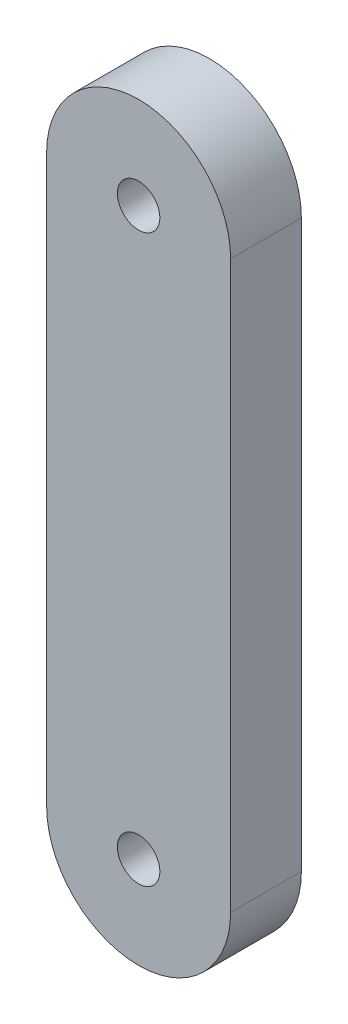
SolidWorks part; units mm, degrees
ref_plane "Front Plane" through (0, 0, 0) normal (0, 0, 1) x (1, 0, 0)
ref_plane "Top Plane" through (0, 0, 0) normal (0, 1, 0) x (1, 0, 0)
ref_plane "Right Plane" through (0, 0, 0) normal (1, 0, 0) x (0, 0, -1)
sketch "Sketch1" plane through (0, 0, 0) normal (0, 0, 1) x (1, 0, 0)
  line L0 (0, 0) -> (0, 20) construction
  line L1 (-3.25, 0) -> (-3.25, 20)
  line L2 (3.25, 0) -> (3.25, 20)
  arc A0 (-3.25, 0) -> (3.25, 0) centre (0, 0) ccw
  arc A1 (3.25, 20) -> (-3.25, 20) centre (0, 20) ccw
  circle A2 centre (0, 20) radius 0.75
  circle A3 centre (0, 0) radius 0.75
  point P2 (0, 10)
  dimension "D2" = 3.25
  dimension "D3" = 1.5
  dimension "D1" = 20
extrude "Boss-Extrude1" add sketch "Sketch1" along normal blind 2.5
